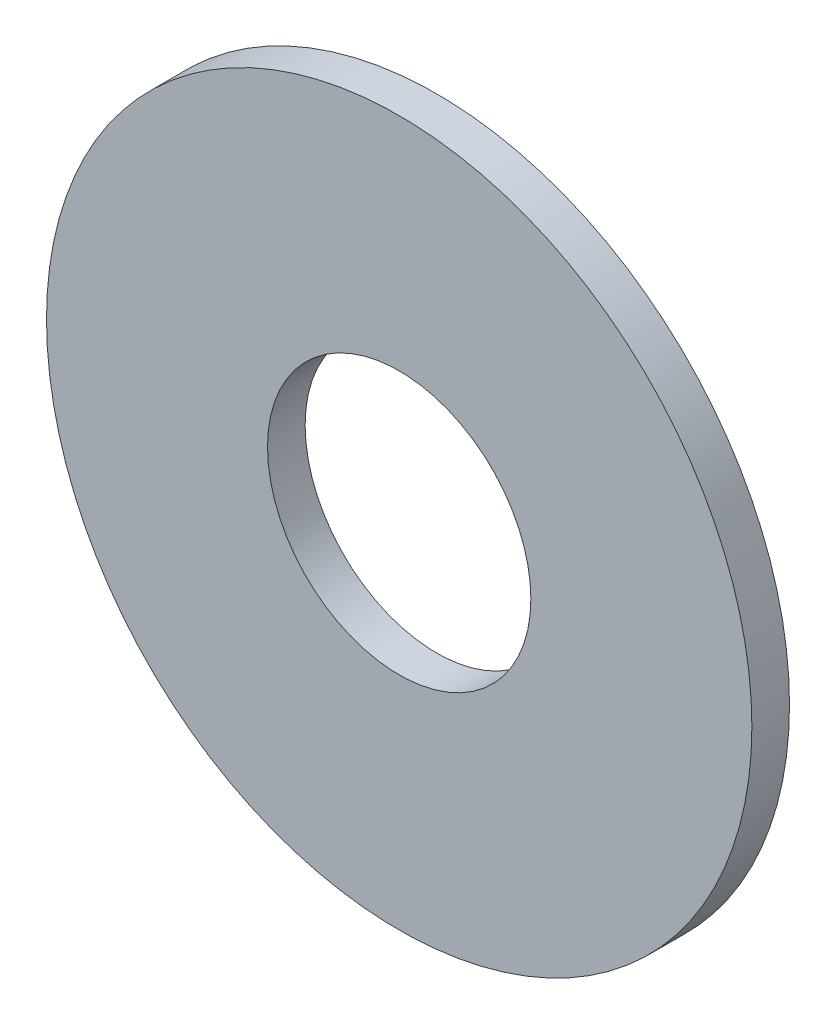
SolidWorks part; units mm, degrees
ref_plane "Front Plane" through (0, 0, 0) normal (0, 0, 1) x (1, 0, 0)
ref_plane "Top Plane" through (0, 0, 0) normal (0, 1, 0) x (1, 0, 0)
ref_plane "Right Plane" through (0, 0, 0) normal (1, 0, 0) x (0, 0, -1)
sketch "Sketch1" plane through (0, 0, 0) normal (0, 0, 1) x (1, 0, 0)
  circle A0 centre (0, 0) radius 1.778
  circle A1 centre (0, 0) radius 4.7625
  dimension "ID" = 3.556
  dimension "OD" = 9.525
extrude "Extrude1" add sketch "Sketch1" against normal blind 0.508
